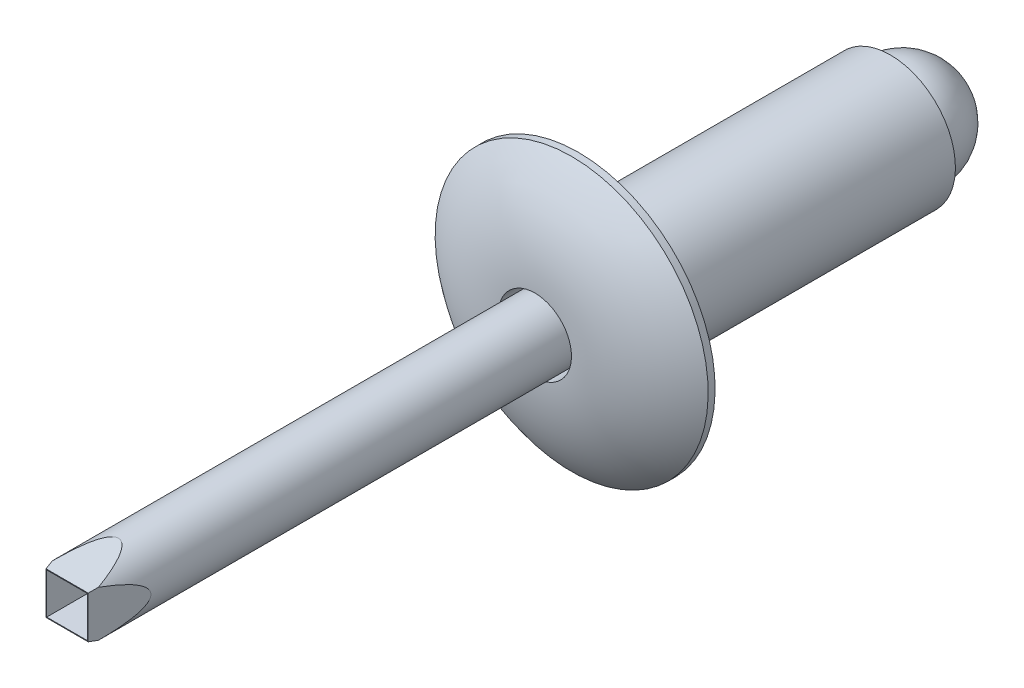
SolidWorks part; units mm, degrees
ref_plane "Front" through (0, 0, 0) normal (0, 0, 1) x (1, 0, 0)
ref_plane "Top" through (0, 0, 0) normal (0, 1, 0) x (1, 0, 0)
ref_plane "Right" through (0, 0, 0) normal (1, 0, 0) x (0, 0, -1)
sketch "Sketch1" plane through (0, 0, 0) normal (1, 0, 0) x (0, 0, -1)
  line L0 (-18.7452, 0) -> (-1.6002, 0) construction
  line L1 (-1.6002, 0) -> (0, 0) construction
  line L2 (0, 0) -> (11.43, 0) construction
  line L3 (11.43, 0) -> (13.8303, 0) construction
  line L8 (0, 5.0038) -> (0, -5.0038) construction
  line L9 (11.43, 2.3813) -> (11.43, -2.3813) construction
  dimension "Length" = 11.43
  dimension "Head Height" = 1.6002
  dimension "D5" = 2.4003
  dimension "D9" = 17.145
  dimension "Diameter" = 4.7625
  dimension "Head Diameter" = 10.0076
sketch "Sketch2" plane through (0, 0, 0) normal (1, 0, 0) x (0, 0, -1)
  line L0 (-18.7452, 1.1906) -> (-18.7452, 0) construction
  line L1 (-18.7452, 1.1906) -> (0, 1.1906) construction
  line L2 (0, 5.0038) -> (0, -5.0038) construction
  line L3 (0, 0) -> (0, 5.0038) construction
  line L4 (-1.6002, 0) -> (-1.6002, -1.8472) construction
  line L5 (11.43, 2.3813) -> (0, 2.3812)
  line L6 (11.43, 2.3813) -> (11.43, 0) construction
  line L7 (13.8303, 0) -> (13.8303, 2.3813) construction
  line L8 (11.43, 2.3813) -> (11.43, 0)
  line L9 (13.8303, 2.3813) -> (11.43, 2.3813) construction
  line L11 (11.43, 0) -> (13.8303, 0) construction
  line L12 (11.43, 0) -> (1.143, 0)
  line L13 (-1.6002, 1.1906) -> (-1.6002, 0) construction
  line L14 (11.43, 2.3813) -> (11.43, 0) construction
  line L15 (11.43, 2.3813) -> (11.43, 0) construction
  line L16 (11.43, 0) -> (11.43, 2.3813) construction
  line L17 (11.43, 2.3813) -> (11.43, 0) construction
  line L18 (11.43, 0) -> (11.43, 2.3813) construction
  line L19 (0, 2.3812) -> (0, 5.0038)
  line L20 (-1.6002, 1.3395) -> (0, 1.3395)
  line L21 (-18.7452, 1.3395) -> (0, 1.3395) construction
  line L22 (0, 5.0038) -> (-0.254, 5.0038)
  line L23 (0, 1.3395) -> (1.143, 1.3395)
  line L24 (1.143, 1.3395) -> (1.143, 0)
  arc A0 (13.8303, 0) -> (11.43, 1.905) centre (11.8742, 0) ccw construction
  arc A2 (-0.254, 5.0038) -> (-1.6002, 1.3395) centre (4.0601, 1.3395) ccw
  dimension "D3" = 0.254
  dimension "D1" = 1.1906
  dimension "D2" = 1.143
  dimension "D5" = 1.905
  dimension "D4" = 0.1488
revolve "Revolve1" add sketch "Sketch2" angle 360 about L12
sketch "Sketch7" plane through (0, 0, 0) normal (1, 0, 0) x (0, 0, -1)
  line L0 (-18.7452, 1.1906) -> (1.143, 1.1906)
  line L1 (1.143, 1.3395) -> (1.143, 0) construction
  line L2 (1.143, 1.1906) -> (1.143, 0)
  line L3 (1.143, 0) -> (-18.7452, 0)
  line L4 (-18.7452, 0) -> (-18.7452, 1.1906)
revolve "Revolve2" add sketch "Sketch7" angle 360 about L0
sketch "Sketch8" plane through (0, 0, 0) normal (1, 0, 0) x (0, 0, -1)
  line L1 (11.43, 1.905) -> (11.43, 0)
  line L2 (11.43, 0) -> (13.8303, 0)
  arc A0 (13.8303, 0) -> (11.43, 1.905) centre (11.8742, 0) ccw construction
  arc A1 (13.8303, 0) -> (11.43, 1.905) centre (11.8742, 0) ccw
revolve "Revolve3" add sketch "Sketch8" angle 360 about L3
sketch "Sketch3" plane through (0, 0, 0) normal (0, 1, 0) x (1, 0, 0)
  line L0 (-1.3938, -15.9489) -> (-0.7739, -18.7452)
  line L2 (-1.1906, -18.7452) -> (1.1906, -18.7452) construction
  line L3 (0, -18.7452) -> (0, -19.2532) construction
  line L4 (-0.7739, -18.7452) -> (0.7739, -18.7452)
  line L5 (-1.3938, -15.9489) -> (-1.3938, -19.2532)
  line L6 (-1.3938, -19.2532) -> (1.3938, -19.2532)
  line L7 (1.3938, -19.2532) -> (1.3938, -15.9489)
  line L8 (-1.1906, 1.143) -> (-1.1906, -18.7452) construction
  line L9 (0, -18.7452) -> (0, -1.6002) construction
  line L10 (0.7739, -18.7452) -> (1.3938, -15.9489)
  point P12 (0, -18.7452)
  dimension "D3" = 0.508
  dimension "D2" = 0.2032
  dimension "D1" = 25
  dimension "D4" = 1.5478
extrude "Cut-Extrude1" cut sketch "Sketch3" against normal through all both and the other way through all
pattern_circular "CirPattern1" count 2 every 90 about axis through (0, 0, 18.7452) along (0, 0, -1) of "Cut-Extrude1"
sketch "Sketch9" plane through (0, 0, 18.7452) normal (0, 0, 1) x (1, 0, 0)
  line L8 (-0.7485, -0.7485) -> (0.7485, -0.7485)
  line L9 (0.7485, -0.7485) -> (0.7485, 0.7485)
  line L10 (0.7485, 0.7485) -> (-0.7485, 0.7485)
  line L11 (-0.7485, 0.7485) -> (-0.7485, -0.7485)
  line L12 (-0.7485, -0.7485) -> (0.7485, -0.7485)
  line L13 (0.7485, -0.7485) -> (0.7485, 0.7485)
  line L14 (0.7485, 0.7485) -> (-0.7485, 0.7485)
  line L15 (-0.7485, 0.7485) -> (-0.7485, -0.7485)
  dimension "D1" = 0.0254
extrude "Cut-Extrude3" cut sketch "Sketch9" against normal blind 2.54
fillet "Fillet2" radius 0.254 1 edges at (0, 2.3812, 0)
ref_plane "Contact Plane 1" through (0, 0, 0) normal (0, 0, -1) x (-1, 0, 0)
equation "\"D5@Sketch1\" = \"Head Height@Sketch1\" * 1.5"
equation "\"D9@Sketch1\" = \"Length@Sketch1\" * 1.5"
equation "\"D1@Sketch2\"=\"Diameter@Sketch1\"/4"
equation "\"D4@Sketch2\"=\"D1@Sketch2\"/8"
equation "\"D2@Sketch2\"=\"Length@Sketch1\"/10"
equation "\"D4@Sketch3\"=\"D1@Sketch2\"*2*.65"
equation "\"D5@Sketch2\"=\"Diameter@Sketch1\"*.8/2"
